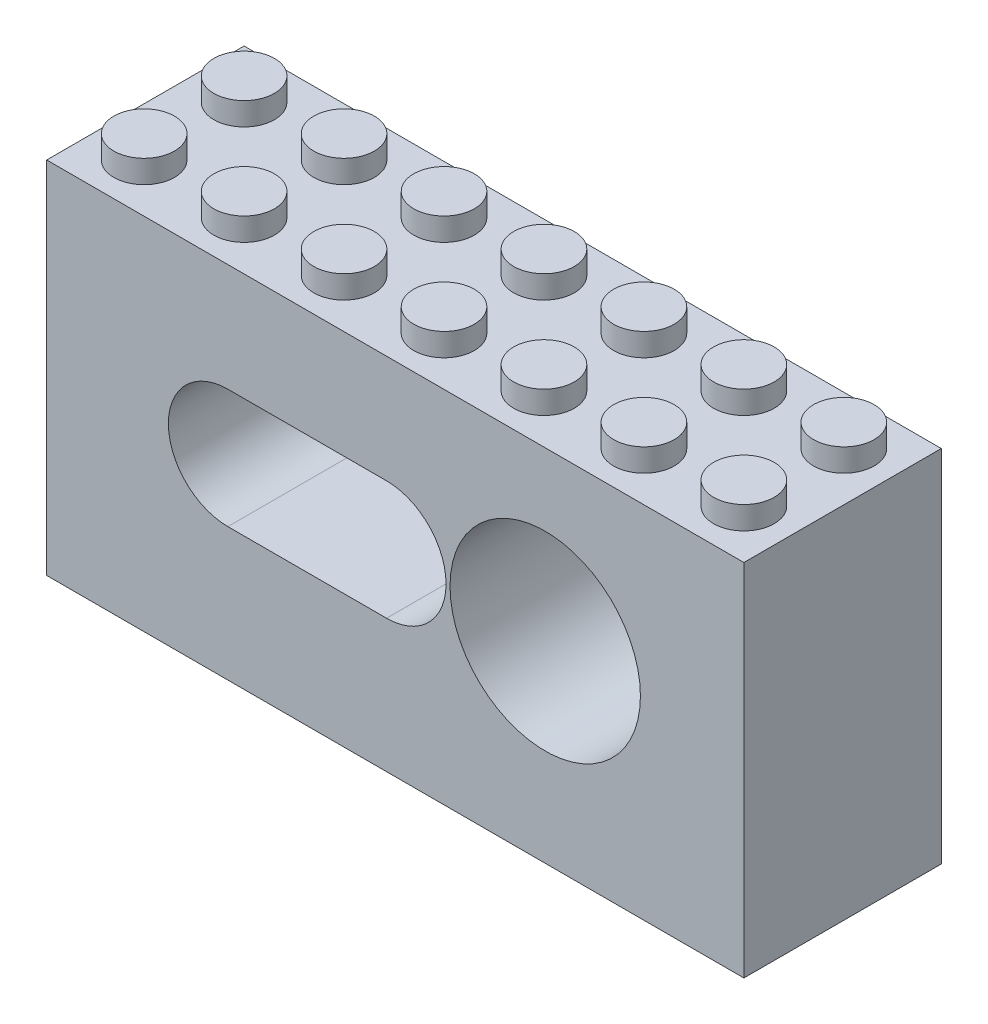
SolidWorks part; units mm, degrees
ref_plane "Front Plane" through (0, 0, 0) normal (0, 0, 1) x (1, 0, 0)
ref_plane "Top Plane" through (0, 0, 0) normal (0, 1, 0) x (1, 0, 0)
ref_plane "Right Plane" through (0, 0, 0) normal (1, 0, 0) x (0, 0, -1)
sketch "Sketch1" plane through (0, 0, 0) normal (0, 1, 0) x (1, 0, 0)
  line L1 (-39.0999, 16.0935) -> (16.7001, 16.0935)
  line L2 (-39.0999, 16.0935) -> (-39.0999, 0.2935)
  line L3 (-39.0999, 0.2935) -> (16.7001, 0.2935)
  line L4 (16.7001, 16.0935) -> (16.7001, 0.2935)
  dimension "D1" = 55.8
  dimension "D2" = 15.8
extrude "Boss-Extrude1" add sketch "Sketch1" along normal blind 28.8
sketch "Sketch2" plane through (0, 0, -0.2935) normal (0, 0, 1) x (1, 0, 0)
  line L0 (-39.0999, 0) -> (16.7001, 0) construction
  line L1 (-11.8999, 15.4) -> (-24.5999, 15.4) construction
  line L2 (-11.8999, 10.6375) -> (-24.5999, 10.6375)
  line L3 (-11.8999, 20.1625) -> (-24.5999, 20.1625)
  line L4 (16.7001, 28.8) -> (16.7001, 0) construction
  circle A0 centre (0.8001, 15.4) radius 7.62
  arc A1 (-11.8999, 10.6375) -> (-11.8999, 20.1625) centre (-11.8999, 15.4) ccw
  arc A2 (-24.5999, 20.1625) -> (-24.5999, 10.6375) centre (-24.5999, 15.4) ccw
  point P6 (-18.2499, 15.4)
  dimension "D4" = 15.24
  dimension "D5" = 4.7625
  dimension "D1" = 15.4
  dimension "D2" = 12.7
  dimension "D3" = 12.7
  dimension "D6" = 15.9
extrude "Cut-Extrude1" cut sketch "Sketch2" against normal blind 12.7
sketch "Sketch4" plane through (0, 0, -16.0935) normal (0, 0, -1) x (-1, 0, 0)
  line L0 (-16.7001, 28.8) -> (-16.7001, 0) construction
  line L1 (-16.7001, 0) -> (39.0999, 0) construction
  circle A6 centre (-0.8001, 15.4) radius 2.7781
  circle A7 centre (11.8999, 15.4) radius 1.8415
  circle A8 centre (24.5999, 15.4) radius 1.8415
  dimension "D1" = 5.5563
  dimension "D2" = 3.683
  dimension "D3" = 3.683
  dimension "D4" = 12.7
  dimension "D5" = 12.7
  dimension "D6" = 15.9
  dimension "D7" = 15.4
extrude "Cut-Extrude2" cut sketch "Sketch4" against normal blind 12.7
sketch "Sketch5" plane through (0, 0, -16.0935) normal (0, 0, -1) x (-1, 0, 0)
  line L2 (24.5999, 20.1625) -> (11.8999, 20.1625)
  line L3 (11.8999, 10.6375) -> (24.5999, 10.6375)
  line L12 (24.5999, 20.1625) -> (11.8999, 20.1625)
  line L13 (11.8999, 10.6375) -> (24.5999, 10.6375)
  arc A2 (11.8999, 20.1625) -> (11.8999, 10.6375) centre (11.8999, 15.4) ccw
  arc A3 (24.5999, 10.6375) -> (24.5999, 20.1625) centre (24.5999, 15.4) ccw
  arc A4 (11.8999, 20.1625) -> (11.8999, 10.6375) centre (11.8999, 15.4) ccw
  arc A5 (24.5999, 10.6375) -> (24.5999, 20.1625) centre (24.5999, 15.4) ccw
  dimension "D2" = 0
extrude "Cut-Extrude6" cut sketch "Sketch5" against normal blind 1.905
sketch "Sketch6" plane through (0, 28.8, 0) normal (0, 1, 0) x (1, 0, 0)
  line L1 (16.7001, 16.0935) -> (-39.0999, 16.0935) construction
  line L3 (16.7001, 0.2935) -> (16.7001, 16.0935) construction
  circle A0 centre (12.8001, 12.1935) radius 2.425
  circle A1 centre (12.8001, 4.1935) radius 2.425
  circle A2 centre (4.8001, 12.1935) radius 2.425
  circle A3 centre (4.8001, 4.1935) radius 2.425
  circle A4 centre (-3.1999, 12.1935) radius 2.425
  circle A5 centre (-3.1999, 4.1935) radius 2.425
  circle A6 centre (-11.1999, 12.1935) radius 2.425
  circle A7 centre (-11.1999, 4.1935) radius 2.425
  circle A8 centre (-19.1999, 12.1935) radius 2.425
  circle A9 centre (-19.1999, 4.1935) radius 2.425
  circle A10 centre (-27.1999, 12.1935) radius 2.425
  circle A11 centre (-27.1999, 4.1935) radius 2.425
  circle A12 centre (-35.1999, 12.1935) radius 2.425
  circle A13 centre (-35.1999, 4.1935) radius 2.425
  dimension "D1" = 4.85
  dimension "D2" = 4.85
  dimension "D3" = 8
  dimension "D5" = 3.9
  dimension "D6" = 3.9
  dimension "D4" = 7
extrude "Boss-Extrude2" add sketch "Sketch6" along normal blind 1.83
sketch "Sketch7" plane through (0, 0, 0) normal (0, -1, 0) x (1, 0, 0)
  line L0 (-39.0999, -16.0935) -> (-39.0999, -0.2935) construction
  line L1 (-37.8799, -1.5135) -> (15.4801, -1.5135)
  line L2 (-37.8799, -1.5135) -> (-37.8799, -14.8735)
  line L3 (-37.8799, -14.8735) -> (15.4801, -14.8735)
  line L4 (15.4801, -1.5135) -> (15.4801, -14.8735)
  line L5 (-39.0999, -0.2935) -> (16.7001, -0.2935) construction
  line L6 (16.7001, -0.2935) -> (16.7001, -16.0935) construction
  line L7 (16.7001, -16.0935) -> (-39.0999, -16.0935) construction
  line L8 (-39.0999, -0.2935) -> (-39.0999, -16.0935)
  circle A0 centre (-31.1999, -8.1935) radius 3.2625
  circle A1 centre (-23.1999, -8.1935) radius 3.2625
  circle A2 centre (-15.1999, -8.1935) radius 3.2625
  circle A3 centre (-7.1999, -8.1935) radius 3.2625
  circle A4 centre (0.8001, -8.1935) radius 3.2625
  circle A5 centre (8.8001, -8.1935) radius 3.2625
  dimension "D5" = 6.525
  dimension "D1" = 1.22
  dimension "D2" = 1.22
  dimension "D3" = 1.22
  dimension "D4" = 1.22
  dimension "D6" = 7.9
  dimension "D7" = 7.9
  dimension "D8" = 15.8
  dimension "D9" = 6
extrude "Cut-Extrude7" cut sketch "Sketch7" against normal blind 3 contours L4 L1 L2 L3 A5 A4 A3 A2 A1 A0
